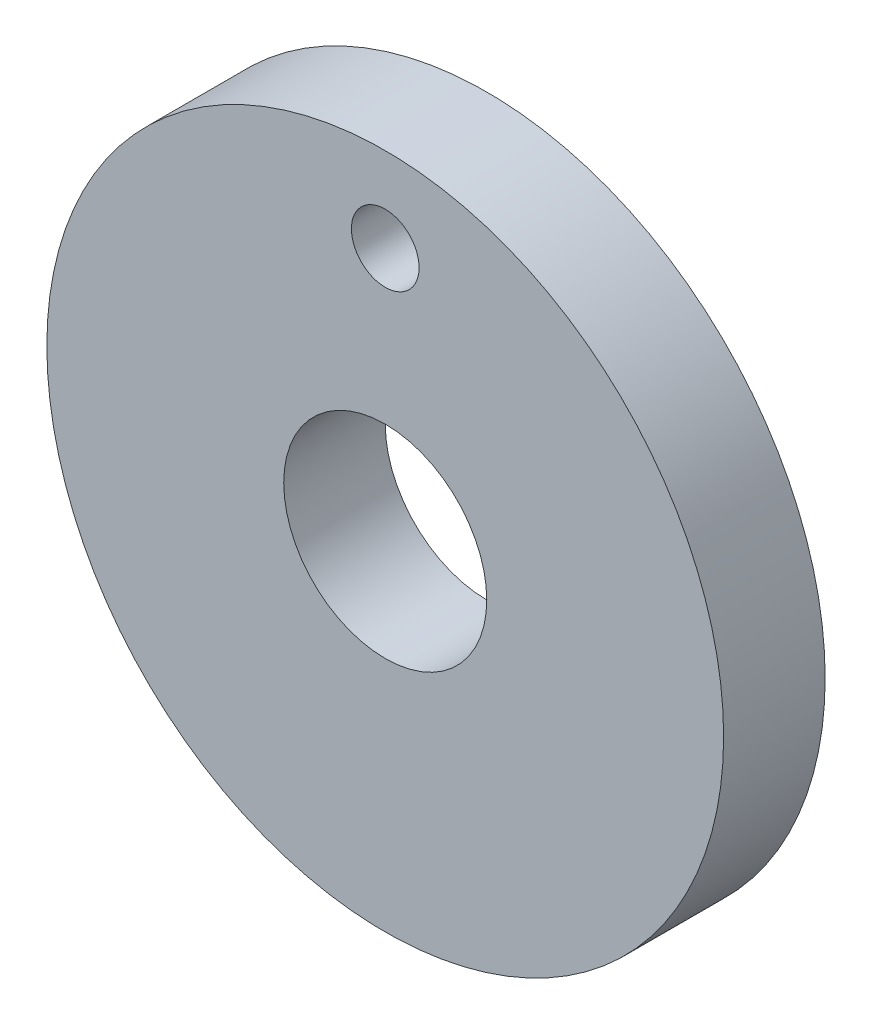
SolidWorks part; units mm, degrees
material "Alliage 1060"
ref_plane "Plan de face" through (0, 0, 0) normal (0, 0, 1) x (1, 0, 0)
ref_plane "Plan de dessus" through (0, 0, 0) normal (0, 1, 0) x (1, 0, 0)
ref_plane "Plan de droite" through (0, 0, 0) normal (1, 0, 0) x (0, 0, -1)
sketch "Esquisse1" plane through (0, 0, 0) normal (0, 0, 1) x (1, 0, 0)
  circle A0 centre (0, 0) radius 10
  circle A1 centre (0, 0) radius 7.5 construction
  circle A2 centre (0, 7.5) radius 1
  circle A3 centre (0, 0) radius 3
  dimension "D1" = 15
  dimension "D2" = 20
  dimension "D3" = 2
  dimension "D4" = 6
extrude "Boss.-Extru.1" add sketch "Esquisse1" along normal blind 3
